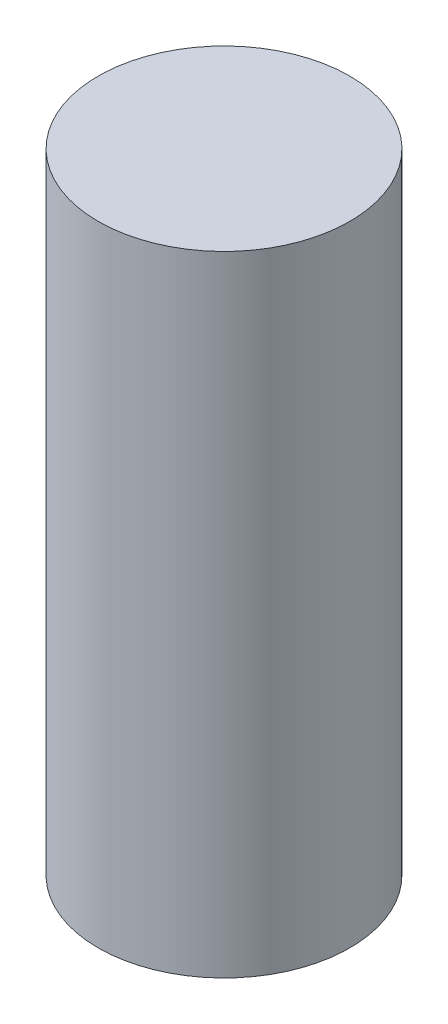
SolidWorks part; units mm, degrees
material "AISI 1020"
ref_plane "Спереди" through (0, 0, 0) normal (0, 0, 1) x (1, 0, 0)
ref_plane "Сверху" through (0, 0, 0) normal (0, 1, 0) x (1, 0, 0)
ref_plane "Справа" through (0, 0, 0) normal (1, 0, 0) x (0, 0, -1)
sketch "Эскиз1" plane through (0, 0, 0) normal (0, 1, 0) x (1, 0, 0)
  circle A0 centre (0, 0) radius 3
  dimension "D1" = 6
extrude "Бобышка-Вытянуть1" add sketch "Эскиз1" along normal blind 15
